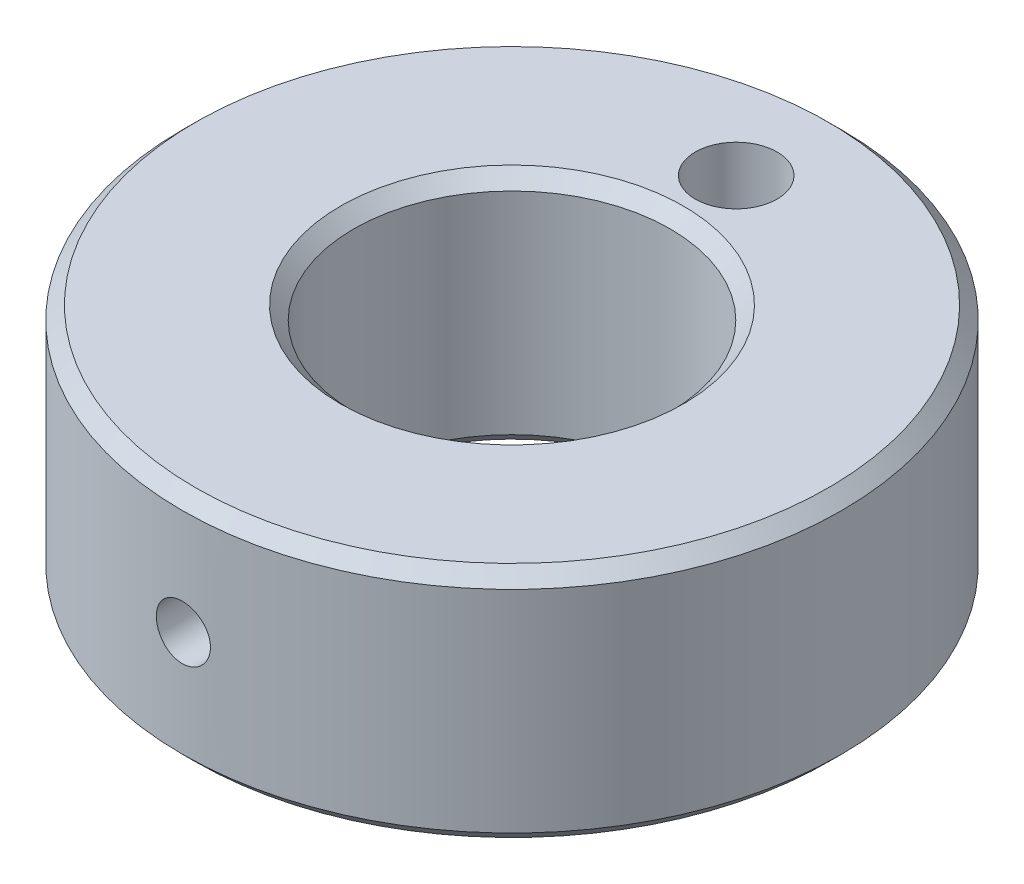
SolidWorks part; units mm, degrees
ref_plane "Front Plane" through (0, 0, 0) normal (0, 0, 1) x (1, 0, 0)
ref_plane "Top Plane" through (0, 0, 0) normal (0, 1, 0) x (1, 0, 0)
ref_plane "Right Plane" through (0, 0, 0) normal (1, 0, 0) x (0, 0, -1)
sketch "Sketch1" plane through (0, 0, 0) normal (0, 1, 0) x (1, 0, 0)
  circle A0 centre (0, 0) radius 12.5
  circle A1 centre (0, 0) radius 6
  dimension "D1" = 25
  dimension "D2" = 12
extrude "Boss-Extrude1" add sketch "Sketch1" along normal blind 9
chamfer "Chamfer1" distance 0.5 angle 45 4 edges at (0, 0, 6) (0, 0, 12.5) (0, 9, 6) (0, 9, 12.5)
ref_plane "Plane1" through (0, 0, 12.5) normal (0, 0, 1) x (1, 0, 0)
sketch "Sketch2" plane through (0, 0, 12.5) normal (0, 0, 1) x (1, 0, 0)
  line L0 (-11.4074, 4.5) -> (8.5516, 4.5) construction
  line L1 (0, 3.6231) -> (0, 5.1596) construction
hole_wizard "M2.5x0.45 Tapped Hole1" positions "Sketch3" profile "Sketch4" tap size "M2.5x0.45" standard "ANSI Metric"
sketch "Sketch3" plane through (0, 0, 12.5) normal (0, 0, 1) x (1, 0, 0)
  line L0 (-11.4074, 4.5) -> (8.5516, 4.5) construction
  line L1 (0, 3.6231) -> (0, 5.1596) construction
  point P0 (0, 4.5)
sketch "Sketch4" plane through (0, 4.5, 12.5) normal (1, 0, 0) x (0, -1, 0)
  line L0 (0, 0) -> (0, 6.5)
  line L1 (0, 6.5) -> (1.025, 6.5)
  line L2 (1.025, 6.5) -> (1.025, 0)
  line L5 (1.025, 0) -> (0, 0)
  line L11 (0, -6.35) -> (0, 107.95) construction
  dimension "Thru Tap Drill Dia." = 2.05
  dimension "Thru Tap Drill Depth" = 6.5
cosmetic thread "Hole Thread1"
sketch "Sketch5" plane through (0, 9, 0) normal (0, 1, 0) x (1, 0, 0)
  line L0 (0, 8.244) -> (0, 11.0194) construction
  circle A0 centre (0, 0) radius 8.5 construction
  dimension "D1" = 17
hole_wizard "Ø3.1 (3.1) Diameter Hole1" positions "Sketch6" profile "Sketch7" hole size "Ø3.1" standard "ANSI Metric"
sketch "Sketch6" plane through (0, 9, 0) normal (0, 1, 0) x (1, 0, 0)
  line L0 (0, 8.244) -> (0, 11.0194) construction
  circle A0 centre (0, 0) radius 8.5 construction
  point P0 (0, 8.5)
sketch "Sketch7" plane through (0, 9, -8.5) normal (1, 0, 0) x (0, 0, 1)
  line L0 (0, 0) -> (0, 3.9313)
  line L1 (0, 3.9313) -> (1.55, 3)
  line L2 (1.55, 3) -> (1.55, 0)
  line L5 (1.55, 0) -> (0, 0)
  line L10 (0, 3.9313) -> (-1.55, 3) construction
  line L11 (0, -6.35) -> (0, 107.95) construction
  dimension "Hole Dia." = 3.1
  dimension "Hole Depth" = 3
  dimension "Drill Angle" = 118
